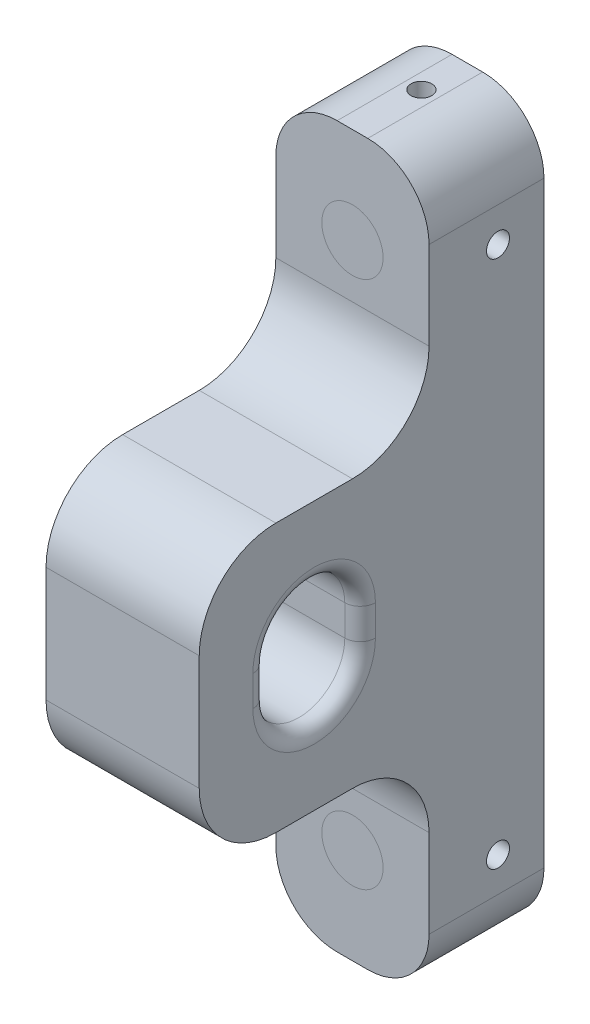
SolidWorks part; units mm, degrees
ref_plane "Front Plane" through (0, 0, 0) normal (0, 0, 1) x (1, 0, 0)
ref_plane "Top Plane" through (0, 0, 0) normal (0, 1, 0) x (1, 0, 0)
ref_plane "Right Plane" through (0, 0, 0) normal (1, 0, 0) x (0, 0, -1)
sketch "Sketch1" plane through (0, 0, 0) normal (0, 0, 1) x (1, 0, 0)
  line L1 (-10, -46.99) -> (10, -46.99)
  line L2 (-10, -46.99) -> (-10, 46.99)
  line L3 (-10, 46.99) -> (10, 46.99)
  line L4 (10, -46.99) -> (10, 46.99)
  line L5 (-10, -46.99) -> (10, 46.99) construction
  line L6 (-10, 46.99) -> (10, -46.99) construction
  point P0 (0, 0)
  dimension "D1" = 20
  dimension "D2" = 93.98
extrude "Boss-Extrude1" add sketch "Sketch1" along normal blind 15
fillet "Fillet1" radius 8 4 edges at (-10, 46.99, 7.5) (-10, -46.99, 7.5) (10, -46.99, 7.5) (10, 46.99, 7.5)
sketch "Sketch2" plane through (0, 0, 15) normal (0, 0, 1) x (1, 0, 0)
  line L0 (0, 46.99) -> (0, -46.99) construction
  line L1 (2, 46.99) -> (-2, 46.99) construction
  line L2 (-2, -46.99) -> (2, -46.99) construction
  circle A1 centre (0, 34.49) radius 4
  circle A2 centre (0, -34.4949) radius 4
extrude "Cut-Extrude1" cut sketch "Sketch2" against normal through all
sketch "Sketch3" plane through (-10, 0, 0) normal (-1, 0, 0) x (0, 0, 1)
  line L0 (6, 46.99) -> (6, -46.99) construction
  line L1 (0, 46.99) -> (15, 46.99) construction
  line L2 (15, -46.99) -> (0, -46.99) construction
  line L3 (15, 38.99) -> (15, 46.99) construction
  line L4 (0, 34.49) -> (6, 34.49) construction
  line L7 (0, 7.99) -> (6, 7.99) construction
  line L8 (0, -34.4949) -> (6, -34.4949) construction
  circle A0 centre (6, 34.49) radius 1.5
  circle A2 centre (6, -34.4949) radius 1.5
  point P8 (15, 42.99)
  dimension "D2" = 3
  dimension "D1" = 9
extrude "Cut-Extrude2" cut sketch "Sketch3" against normal through all
sketch "Sketch4" plane through (-10, 0, 0) normal (-1, 0, 0) x (0, 0, 1)
  line L0 (15, 38.99) -> (15, -38.99) construction
  line L1 (15, 17.5) -> (45, 17.5)
  line L2 (15, 17.5) -> (15, -17.5)
  line L3 (15, -17.5) -> (45, -17.5)
  line L4 (45, 17.5) -> (45, -17.5)
  line L5 (0, 0) -> (15, 0) construction
  dimension "D1" = 35
  dimension "D2" = 17.5
  dimension "D3" = 30
extrude "Boss-Extrude2" add sketch "Sketch4" against normal up to surface (20 mm away) up to face at (10, 34.49, 7.5)
fillet "Fillet2" radius 10 4 edges at (0, 17.5, 45) (0, -17.5, 45) (0, -17.5, 15) (0, 17.5, 15)
sketch "Sketch5" plane through (10, 0, 0) normal (1, 0, 0) x (0, 0, -1)
  line L0 (-30, 17.5) -> (-30, -17.5) construction
  line L1 (-25, 17.5) -> (-35, 17.5) construction
  line L2 (-35, -17.5) -> (-25, -17.5) construction
  line L3 (-30, 2) -> (-30, -2) construction
  line L4 (-24, 2) -> (-24, -2)
  line L5 (-36, 2) -> (-36, -2)
  arc A0 (-24, 2) -> (-36, 2) centre (-30, 2) ccw
  arc A1 (-36, -2) -> (-24, -2) centre (-30, -2) ccw
  point P8 (-30, 0)
  dimension "D3" = 6
  dimension "D1" = 17.5
  dimension "D2" = 2
extrude "Cut-Extrude3" cut sketch "Sketch5" against normal through all
fillet "Fillet3" radius 2 8 edges at (-10, 8, 30) (-10, 0, 24) (-10, -8, 30) (10, 8, 30) (10, 0, 24) (10, -8, 30) (-10, 0, 36) (10, 0, 36)
sketch "Sketch6" plane through (0, 46.99, 0) normal (0, 1, 0) x (1, 0, 0)
  line L0 (0, -15) -> (0, 0) construction
  line L1 (-10, -15) -> (10, -15) construction
  circle A0 centre (0, -6) radius 1.35
  dimension "D1" = 2.7
  dimension "D2" = 9
extrude "Cut-Extrude4" cut sketch "Sketch6" against normal blind 10
mirror "Mirror1" about plane through (0, 0, 0) normal (0, 1, 0) of "Cut-Extrude4"
sketch "Sketch7" plane through (0, 0, 15) normal (0, 0, 1) x (1, 0, 0)
  circle A1 centre (0, 34.49) radius 4
  circle A2 centre (0, -34.4949) radius 4
extrude "Boss-Extrude3" add sketch "Sketch7" against normal blind 2 separate body
